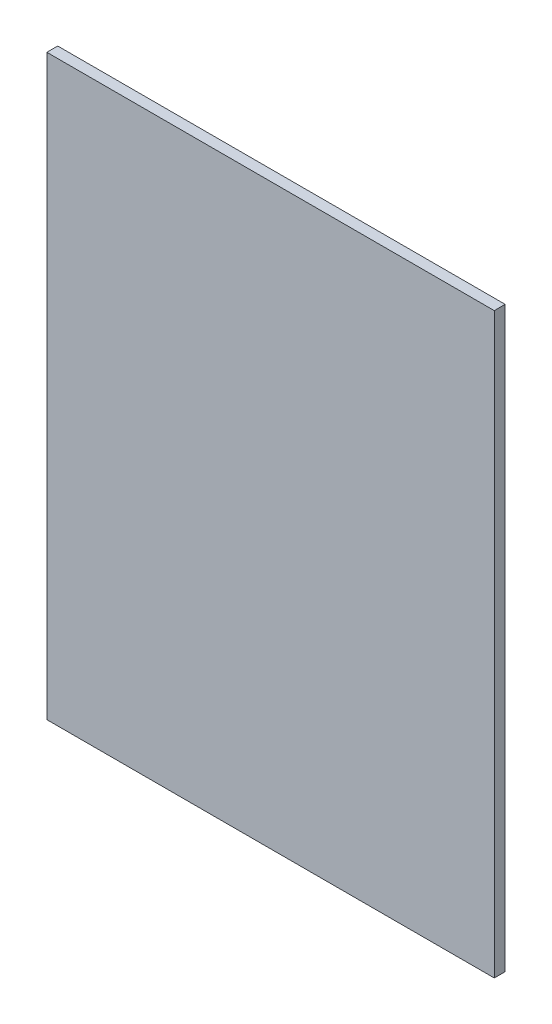
SolidWorks part; units mm, degrees
ref_plane "Front Plane" through (0, 0, 0) normal (0, 0, 1) x (1, 0, 0)
ref_plane "Top Plane" through (0, 0, 0) normal (0, 1, 0) x (1, 0, 0)
ref_plane "Right Plane" through (0, 0, 0) normal (1, 0, 0) x (0, 0, -1)
sketch "Sketch1" plane through (0, 0, 0) normal (0, 0, 1) x (1, 0, 0)
  line L1 (0, 0) -> (658, 0)
  line L2 (0, 0) -> (0, 850)
  line L3 (0, 850) -> (658, 850)
  line L4 (658, 0) -> (658, 850)
  dimension "D1" = 658
  dimension "D2" = 850
extrude "Extrude1" add sketch "Sketch1" along normal blind 16
